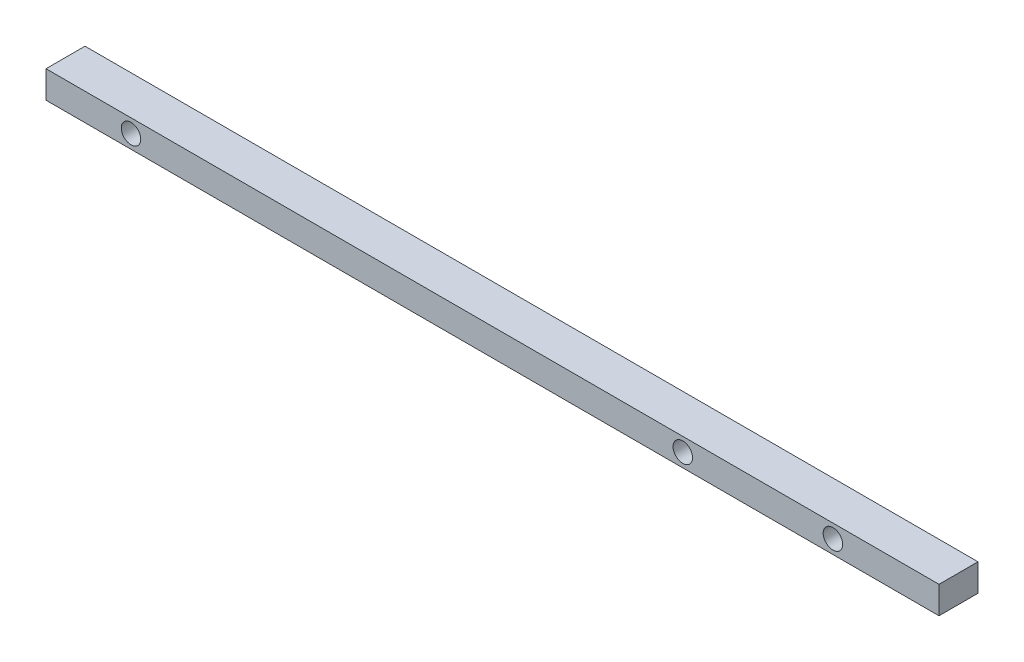
SolidWorks part; units mm, degrees
ref_plane "Front Plane" through (0, 0, 0) normal (0, 0, 1) x (1, 0, 0)
ref_plane "Top Plane" through (0, 0, 0) normal (0, 1, 0) x (1, 0, 0)
ref_plane "Right Plane" through (0, 0, 0) normal (1, 0, 0) x (0, 0, -1)
sketch "Sketch5" plane through (0, 0, 0) normal (1, 0, 0) x (0, 0, -1)
  line L1 (0, 0) -> (2.54, 0)
  line L2 (0, 0) -> (0, 1.778)
  line L3 (0, 1.778) -> (2.54, 1.778)
  line L4 (2.54, 0) -> (2.54, 1.778)
  dimension "D1" = 1.778
  dimension "D2" = 2.54
extrude "Boss-Extrude3" add sketch "Sketch5" along normal blind 58.166
sketch "Sketch6" plane through (0, 0, 0) normal (0, 0, 1) x (1, 0, 0)
  line L0 (0, 0.889) -> (58.166, 0.889) construction
  line L1 (0, 1.778) -> (0, 0) construction
  line L2 (58.166, 1.778) -> (58.166, 0) construction
  circle A0 centre (5.5372, 0.889) radius 0.635
  dimension "D1" = 1.27
  dimension "D2" = 5.5372
extrude "Cut-Extrude3" cut sketch "Sketch6" against normal through all
sketch "Sketch8" plane through (0, 0, 0) normal (0, 0, 1) x (1, 0, 0)
  line L0 (0, 0.889) -> (58.166, 0.889) construction
  line L1 (0, 1.778) -> (0, 0) construction
  line L2 (58.166, 1.778) -> (58.166, 0) construction
  circle A0 centre (41.4782, 0.889) radius 0.635
  circle A1 centre (5.5372, 0.889) radius 0.635 construction
  circle A2 centre (51.2572, 0.889) radius 0.635
  dimension "D1" = 1.27
  dimension "D2" = 35.941
  dimension "D3" = 1.27
  dimension "D4" = 45.72
extrude "Cut-Extrude4" cut sketch "Sketch8" against normal through all
